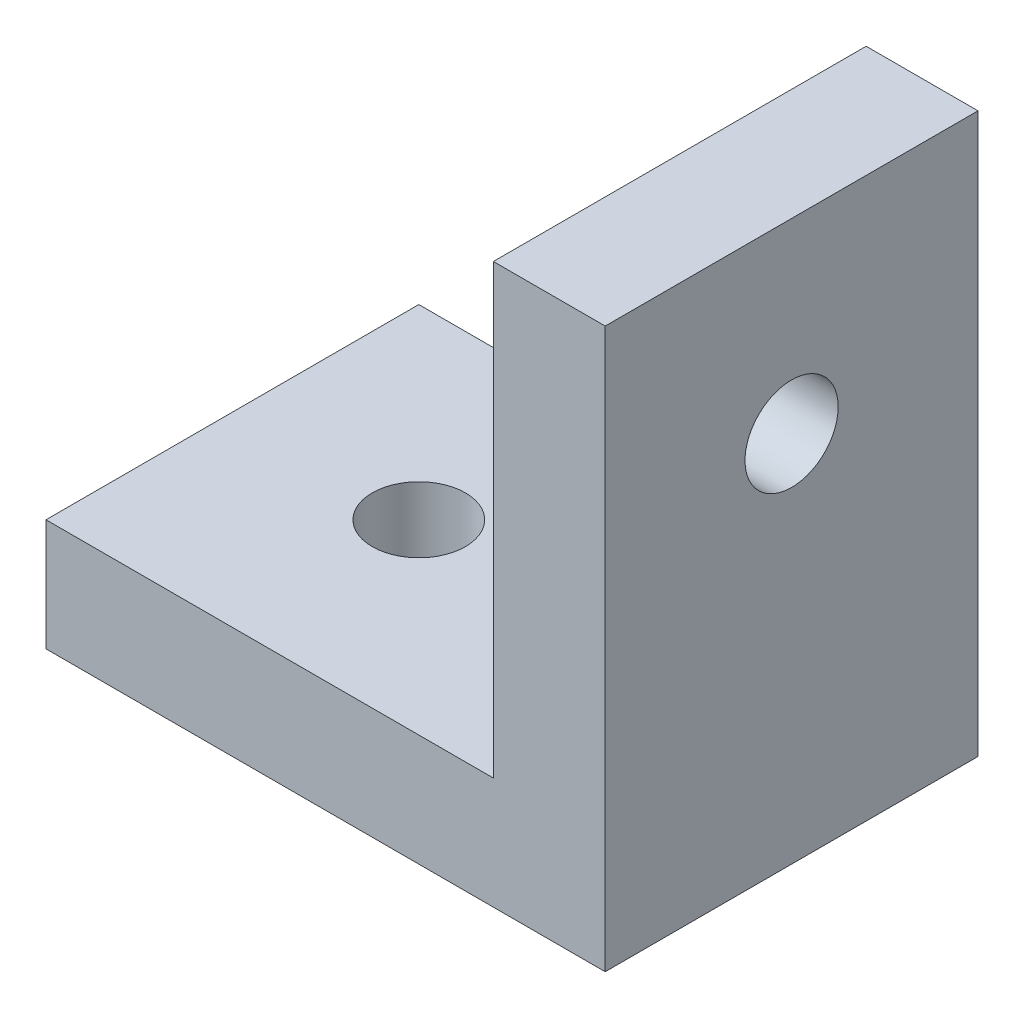
SolidWorks part; units mm, degrees
ref_plane "前基準面" through (0, 0, 0) normal (0, 0, 1) x (1, 0, 0)
ref_plane "上基準面" through (0, 0, 0) normal (0, 1, 0) x (1, 0, 0)
ref_plane "右基準面" through (0, 0, 0) normal (1, 0, 0) x (0, 0, -1)
ref_plane "平面1" through (0, 0, -5) normal (0, 0, -1) x (-1, 0, 0)
sketch "草圖1" plane through (0, 0, -5) normal (0, 0, -1) x (-1, 0, 0)
  line L0 (-7.5, 0) -> (7.5, 0)
  line L1 (7.5, 0) -> (7.5, 3)
  line L2 (7.5, 3) -> (-4.5, 3)
  line L3 (-4.5, 3) -> (-4.5, 15)
  line L4 (-4.5, 15) -> (-7.5, 15)
  line L5 (-7.5, 15) -> (-7.5, 0)
extrude "填料-伸長1" add sketch "草圖1" against normal blind 10
hole_wizard "Ø2.5 (2.5) 直徑孔1" positions "草圖3" profile "草圖2" hole size "Ø2.5" standard "Ansi Metric"
sketch "草圖3" plane through (7.5, 0, 0) normal (1, 0, 0) x (0, 0, -1)
  point P0 (0, 10)
sketch "草圖2" plane through (7.5, 10, 0) normal (0, 1, 0) x (0, 0, -1)
  line L0 (0, 0) -> (0, 15)
  line L1 (0, 15) -> (1.25, 15)
  line L2 (1.25, 15) -> (1.25, 0)
  line L5 (1.25, 0) -> (0, 0)
  line L11 (0, -6.35) -> (0, 107.95) construction
  dimension "砮 ふ 畖" = 2.5
  dimension "砮 ふ瞏 " = 15
hole_wizard "Ø2.5 (2.5) 直徑孔2" positions "草圖5" profile "草圖4" hole size "Ø2.5" standard "Ansi Metric"
sketch "草圖5" plane through (0, 0, 0) normal (0, -1, 0) x (-1, 0, 0)
  point P0 (2.5, 0)
sketch "草圖4" plane through (-2.5, 0, 0) normal (1, 0, 0) x (0, 0, -1)
  line L0 (0, 0) -> (0, 15)
  line L1 (0, 15) -> (1.25, 15)
  line L2 (1.25, 15) -> (1.25, 0)
  line L5 (1.25, 0) -> (0, 0)
  line L11 (0, -6.35) -> (0, 107.95) construction
  dimension "砮 ふ 畖" = 2.5
  dimension "砮 ふ瞏 " = 15
